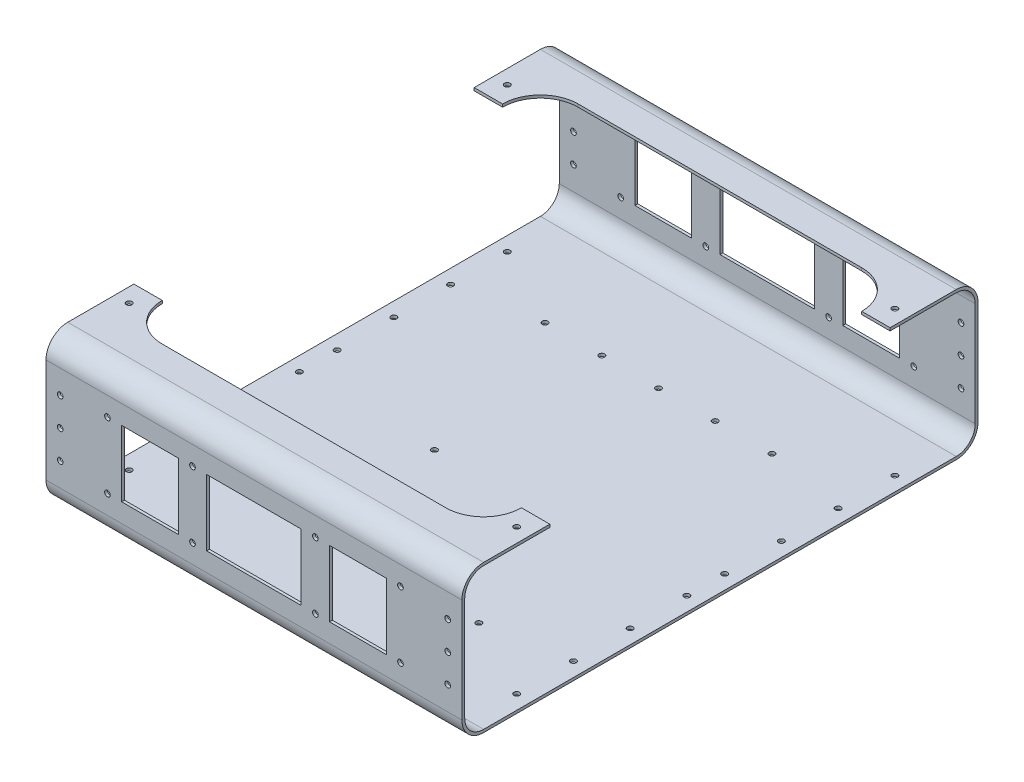
SolidWorks part; units mm, degrees
ref_plane "Front Plane" through (0, 0, 0) normal (0, 0, 1) x (1, 0, 0)
ref_plane "Top Plane" through (0, 0, 0) normal (0, 1, 0) x (1, 0, 0)
ref_plane "Right Plane" through (0, 0, 0) normal (1, 0, 0) x (0, 0, -1)
sketch "Sketch1" plane through (0, 0, 0) normal (1, 0, 0) x (0, 0, -1)
  line L0 (-125, 39) -> (125, 39)
  line L1 (-125, 37.5) -> (125, 37.5)
  line L2 (-135, 27.5) -> (-135, -27.5)
  line L3 (-125, -37.5) -> (125, -37.5)
  line L4 (135, 27.5) -> (135, -27.5)
  line L5 (-135, 37.5) -> (135, -37.5) construction
  line L6 (-135, -37.5) -> (135, 37.5) construction
  line L7 (136.5, 27.5) -> (136.5, -27.5)
  line L8 (-125, -39) -> (125, -39)
  line L9 (-136.5, 27.5) -> (-136.5, -27.5)
  arc A0 (125, 37.5) -> (135, 27.5) centre (125, 27.5) cw
  arc A1 (125, -37.5) -> (135, -27.5) centre (125, -27.5) ccw
  arc A2 (-135, -27.5) -> (-125, -37.5) centre (-125, -27.5) ccw
  arc A3 (-125, 37.5) -> (-135, 27.5) centre (-125, 27.5) ccw
  arc A4 (125, 39) -> (136.5, 27.5) centre (125, 27.5) cw
  arc A5 (125, -39) -> (136.5, -27.5) centre (125, -27.5) ccw
  arc A6 (-136.5, -27.5) -> (-125, -39) centre (-125, -27.5) ccw
  arc A7 (-125, 39) -> (-136.5, 27.5) centre (-125, 27.5) ccw
  point P0 (0, 0)
  dimension "D1" = 10
  dimension "D2" = 1.5
extrude "Boss-Extrude1" add sketch "Sketch1" along normal blind 220
sketch "Sketch2" plane through (0, 39, 0) normal (0, 1, 0) x (1, 0, 0)
  line L0 (110, 125) -> (110, -125) construction
  line L1 (220, 125) -> (0, 125) construction
  line L2 (220, -125) -> (0, -125) construction
  line L3 (0, 0) -> (220, 0) construction
  line L4 (220, 125) -> (220, -125) construction
  line L5 (15, 90) -> (0, 90)
  line L6 (35, 110) -> (185, 110)
  line L7 (205, 90) -> (220, 90)
  line L8 (35, -110) -> (185, -110)
  line L10 (15, 110) -> (205, -110) construction
  line L11 (15, -110) -> (205, 110) construction
  line L12 (0, 125) -> (0, -125) construction
  line L13 (0, 90) -> (0, -90)
  line L14 (0, -90) -> (15, -90)
  line L15 (220, 90) -> (220, -90)
  line L16 (220, -90) -> (205, -90)
  arc A0 (35, 110) -> (15, 90) centre (35, 90) ccw
  arc A1 (185, 110) -> (205, 90) centre (185, 90) cw
  arc A2 (185, -110) -> (205, -90) centre (185, -90) ccw
  arc A3 (15, -90) -> (35, -110) centre (35, -90) ccw
  point P11 (110, 0)
  dimension "D1" = 20
extrude "Cut-Extrude1" cut sketch "Sketch2" against normal blind 10
sketch "Sketch3" plane through (0, 0, 136.5) normal (0, 0, 1) x (1, 0, 0)
  line L0 (110, 27.5) -> (110, -27.5) construction
  line L1 (220, 27.5) -> (0, 27.5) construction
  line L2 (220, -27.5) -> (0, -27.5) construction
  line L3 (0, 0) -> (220, 0) construction
  line L4 (0, 27.5) -> (0, -27.5) construction
  line L5 (220, 27.5) -> (220, -27.5) construction
  line L6 (40, 17.5) -> (70, 17.5)
  line L7 (70, 17.5) -> (70, -17.5)
  line L8 (40, 17.5) -> (32.5, 17.5) construction
  line L9 (40, -17.5) -> (70, -17.5)
  line L10 (180, 17.5) -> (187.5, 17.5) construction
  line L11 (20, 17.5) -> (200, -17.5) construction
  line L12 (20, -17.5) -> (200, 17.5) construction
  line L13 (180, 17.5) -> (150, 17.5)
  line L14 (150, 17.5) -> (150, -17.5)
  line L15 (85, -17.5) -> (135, -17.5)
  line L16 (85, 17.5) -> (135, 17.5)
  line L17 (135, 17.5) -> (135, -17.5)
  line L18 (85, 17.5) -> (85, -17.5)
  line L19 (150, -17.5) -> (180, -17.5)
  line L20 (70, 17.5) -> (85, 17.5) construction
  line L21 (70, -17.5) -> (85, -17.5) construction
  line L22 (135, -17.5) -> (150, -17.5) construction
  line L23 (135, 17.5) -> (150, 17.5) construction
  line L26 (150, 17.5) -> (150, 27.5) construction
  line L27 (220, 27.5) -> (0, 27.5) construction
  line L28 (150, 27.5) -> (180, 27.5) construction
  line L29 (180, 17.5) -> (180, -17.5)
  line L31 (40, 17.5) -> (40, -17.5)
  circle A0 centre (77.5, 17.5) radius 1.5
  circle A1 centre (77.5, -17.5) radius 1.5
  circle A2 centre (142.5, 17.5) radius 1.5
  circle A3 centre (142.5, -17.5) radius 1.5
  circle A4 centre (32.5, 17.5) radius 1.5
  circle A5 centre (32.5, -17.5) radius 1.5
  circle A6 centre (187.5, 17.5) radius 1.5
  circle A7 centre (187.5, -17.5) radius 1.5
  point P12 (110, 0)
extrude "Cut-Extrude2" cut sketch "Sketch3" against normal through all
sketch "Sketch5" plane through (0, -37.5, 0) normal (0, 1, 0) x (1, 0, 0)
  line L0 (0, -125) -> (79, -125) construction
  line L1 (220, -125) -> (0, -125) construction
  line L2 (79, -125) -> (79, -55) construction
  line L3 (79, -55) -> (79, -10) construction
  circle A0 centre (79, -55) radius 1.5
  circle A1 centre (79, -10) radius 1.5
extrude "Cut-Extrude3" cut sketch "Sketch5" against normal blind 10
sketch "Sketch6" plane through (0, -37.5, 0) normal (0, 1, 0) x (1, 0, 0)
  line L0 (110, -136.5) -> (110, -77.5) construction
  line L1 (220, -136.5) -> (0, -136.5) construction
  line L2 (0, 0) -> (220, 0) construction
  line L3 (220, -125) -> (220, 125) construction
  line L4 (110, 136.5) -> (110, 77.5) construction
  line L5 (220, 136.5) -> (0, 136.5) construction
  circle A0 centre (110, -77.5) radius 1.5
  circle A1 centre (140, -77.5) radius 1.5
  circle A2 centre (170, -77.5) radius 1.5
  circle A3 centre (80, -77.5) radius 1.5
  circle A4 centre (50, -77.5) radius 1.5
  circle A5 centre (110, 77.5) radius 1.5
  circle A6 centre (140, 77.5) radius 1.5
  circle A7 centre (170, 77.5) radius 1.5
  circle A8 centre (80, 77.5) radius 1.5
  circle A9 centre (50, 77.5) radius 1.5
  dimension "D1" = 3
  dimension "D3" = 3
  dimension "D2" = 3
  dimension "D4" = 3
extrude "Cut-Extrude4" cut sketch "Sketch6" against normal blind 10
sketch "Sketch7" plane through (0, -37.5, 0) normal (0, 1, 0) x (1, 0, 0)
  line L0 (0, 0) -> (15, 0) construction
  line L1 (0, -125) -> (0, 125) construction
  line L2 (7.5, 0) -> (7.5, 10) construction
  line L3 (7.5, 0) -> (7.5, -10) construction
  circle A0 centre (7.5, 10) radius 1.5
  circle A1 centre (7.5, -10) radius 1.5
  circle A2 centre (7.5, -40) radius 1.5
  circle A3 centre (7.5, -70) radius 1.5
  circle A4 centre (7.5, -100) radius 1.5
  circle A5 centre (7.5, 40) radius 1.5
  circle A6 centre (7.5, 70) radius 1.5
  circle A7 centre (7.5, 100) radius 1.5
  dimension "D1" = 4
  dimension "D2" = 4
extrude "Cut-Extrude5" cut sketch "Sketch7" against normal through all and the other way through all
sketch "Sketch8" plane through (0, -39, 0) normal (0, -1, 0) x (1, 0, 0)
  line L0 (220, 0) -> (205, 0) construction
  line L1 (220, 125) -> (220, -125) construction
  line L2 (212.5, 0) -> (212.5, 10) construction
  line L3 (212.5, 0) -> (212.5, -10) construction
  circle A0 centre (212.5, 10) radius 1.5
  circle A1 centre (212.5, -10) radius 1.5
  circle A2 centre (212.5, -40) radius 1.5
  circle A3 centre (212.5, -70) radius 1.5
  circle A4 centre (212.5, -100) radius 1.5
  circle A5 centre (212.5, 40) radius 1.5
  circle A6 centre (212.5, 70) radius 1.5
  circle A7 centre (212.5, 100) radius 1.5
  dimension "D1" = 4
  dimension "D2" = 4
extrude "Cut-Extrude6" cut sketch "Sketch8" against normal through all
sketch "Sketch9" plane through (0, 0, -136.5) normal (0, 0, -1) x (-1, 0, 0)
  line L0 (0, 0) -> (-15, 0) construction
  line L1 (-7.5, 0) -> (-7.5, 15) construction
  line L2 (-7.5, 0) -> (-7.5, -15) construction
  line L3 (-220, 0) -> (-205, 0) construction
  line L4 (-220, -27.5) -> (-220, 27.5) construction
  circle A0 centre (-7.5, 0) radius 1.5
  circle A1 centre (-7.5, 15) radius 1.5
  circle A2 centre (-7.5, -15) radius 1.5
  circle A3 centre (-212.5, 0) radius 1.5
  circle A4 centre (-212.5, 15) radius 1.5
  circle A5 centre (-212.5, -15) radius 1.5
extrude "Cut-Extrude7" cut sketch "Sketch9" against normal through all
